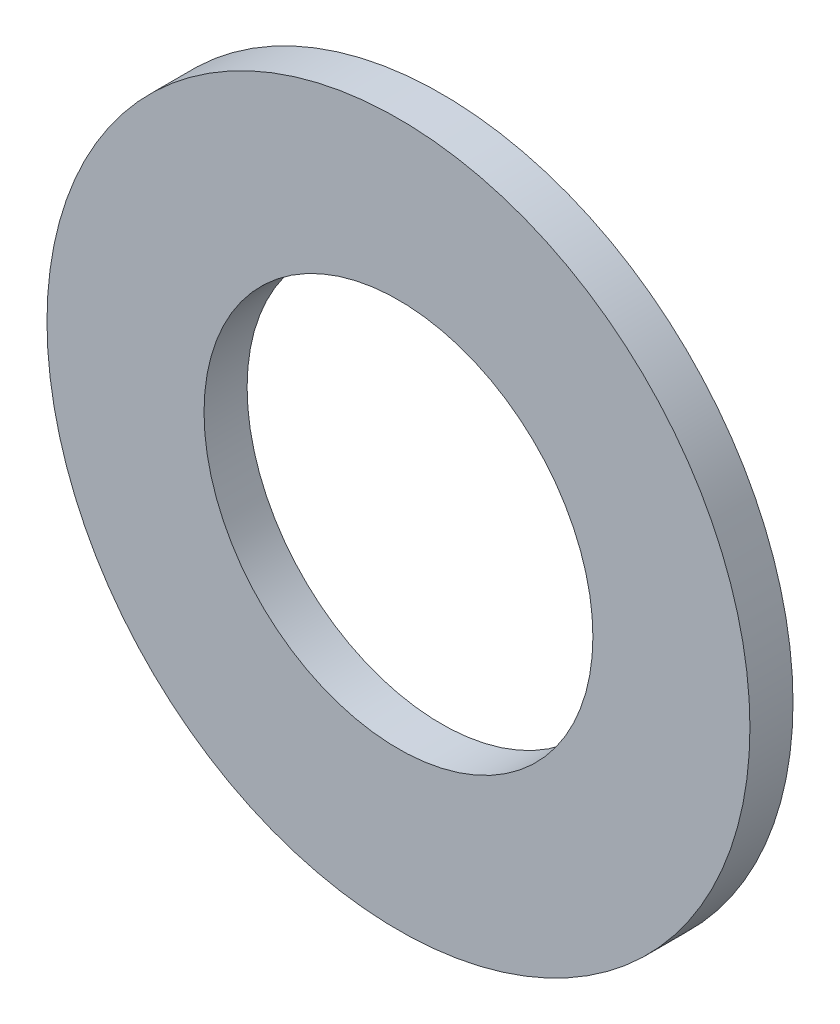
SolidWorks part; units mm, degrees
ref_plane "Front Plane" through (0, 0, 0) normal (0, 0, 1) x (1, 0, 0)
ref_plane "Top Plane" through (0, 0, 0) normal (0, 1, 0) x (1, 0, 0)
ref_plane "Right Plane" through (0, 0, 0) normal (1, 0, 0) x (0, 0, -1)
sketch "Sketch1" plane through (0, 0, 0) normal (0, 0, 1) x (1, 0, 0)
  circle A0 centre (0, 0) radius 10.3187
  circle A1 centre (0, 0) radius 18.6531
  dimension "ID" = 20.6375
  dimension "OD" = 37.3062
extrude "Extrude1" add sketch "Sketch1" against normal blind 2.286
